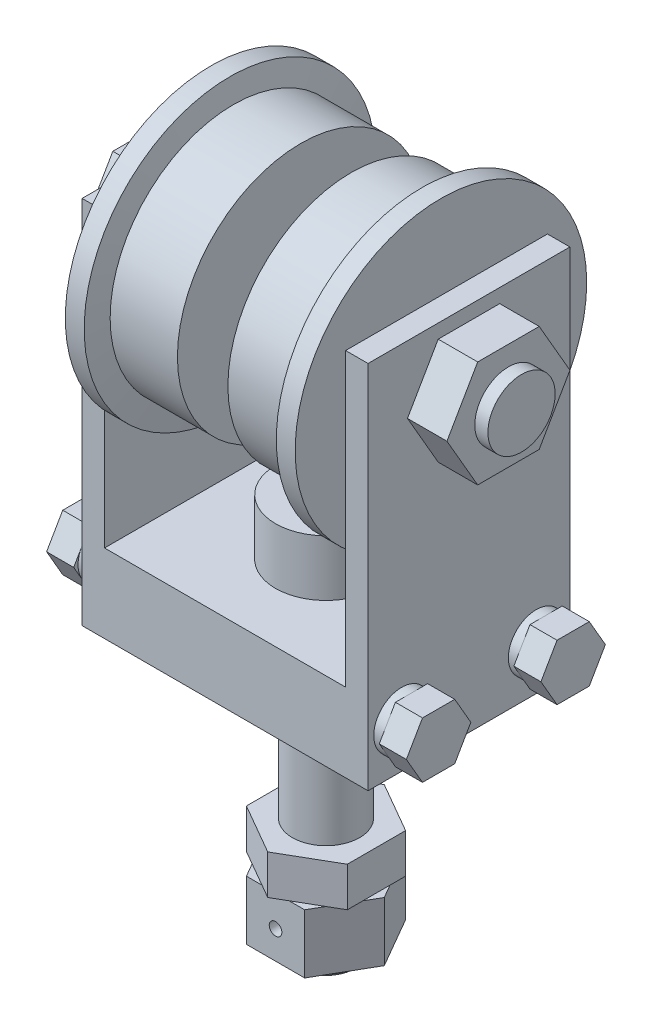
SolidWorks part; units mm, degrees
ref_plane "Front" through (0, 0, 0) normal (0, 0, 1) x (1, 0, 0)
ref_plane "Top" through (0, 0, 0) normal (0, 1, 0) x (1, 0, 0)
ref_plane "Right" through (0, 0, 0) normal (1, 0, 0) x (0, 0, -1)
ref_plane "Z PLANE" through (0, 0, 0) normal (0, 0, 1) x (1, 0, 0)
ref_plane "YOKE BOTTOM" through (0, 0, 0) normal (0, 1, 0) x (-1, 0, 0)
ref_plane "X PLANE" through (0, 0, 0) normal (1, 0, 0) x (0, 0, -1)
sketch "YOKE CROSS SECTION" plane through (0, 0, 0) normal (1, 0, 0) x (0, 0, -1)
  line L0 (0, 0) -> (0, 57.0916) construction
  line L1 (0, 84.8167) -> (0, -84.8167) construction
  line L2 (-57.15, 0) -> (57.15, 0)
  line L3 (69.1602, 0) -> (-69.1602, 0) construction
  line L4 (57.15, 0) -> (57.15, 44.45)
  line L5 (-57.15, 0) -> (-57.15, 44.45)
  line L6 (57.15, 44.45) -> (-57.15, 44.45)
  point P12 (0, 44.45)
  dimension "D1" = 44.45
  dimension "D2" = 114.3
ref_plane "1/2 YOKE LENGTH (A)" through (68.2625, 0, 0) normal (1, 0, 0) x (0, 0, -1)
extrude "YOKE" add sketch "YOKE CROSS SECTION" along normal up to surface (68.2625 mm away) up to plane "1/2 YOKE LENGTH (A)"
sketch "SIDEPLATE PROFILE" plane through (68.2625, 0, 0) normal (1, 0, 0) x (0, 0, -1)
  line L0 (0, 0) -> (0, 74.7424) construction
  line L1 (0, 84.8167) -> (0, -84.8167) construction
  line L2 (-57.15, 0) -> (57.15, 0)
  line L3 (57.15, 0) -> (57.15, 209.55)
  line L4 (-57.15, 0) -> (-57.15, 209.55)
  line L5 (57.15, 209.55) -> (-57.15, 209.55)
  point P11 (0, 209.55)
  dimension "D1" = 209.55
ref_plane "WHEEL HEIGHT" through (0, 171.45, 0) normal (0, 1, 0) x (-1, 0, 0)
ref_plane "SCREW LOCATION X" through (0, 0, 38.1) normal (0, 0, 1) x (1, 0, 0)
ref_plane "SCREW LOCATION Y" through (0, 25.4, 0) normal (0, 1, 0) x (-1, 0, 0)
extrude "SIDEPLATE" add sketch "SIDEPLATE PROFILE" along normal blind 12.7
sketch "WHEEL PIN NUT PROFILE" plane through (80.9625, 0, 0) normal (1, 0, 0) x (0, 0, -1)
  line L0 (0, 84.8167) -> (0, -84.8167) construction
  line L1 (34.8287, 171.45) -> (17.4143, 201.6125)
  line L2 (17.4143, 201.6125) -> (-17.4143, 201.6125)
  line L3 (-17.4143, 201.6125) -> (-34.8287, 171.45)
  line L4 (-34.8287, 171.45) -> (-17.4143, 141.2875)
  line L5 (-17.4143, 141.2875) -> (17.4143, 141.2875)
  line L6 (17.4143, 141.2875) -> (34.8287, 171.45)
  line L7 (69.1602, 171.45) -> (-69.1602, 171.45) construction
  circle A0 centre (0, 171.45) radius 30.1625 construction
  dimension "D1" = 60.325
extrude "WHEEL PIN NUT" add sketch "WHEEL PIN NUT PROFILE" along normal blind 22.352
sketch "WHEEL PIN PROJECTION PROFILE" plane through (103.3145, 0, 0) normal (1, 0, 0) x (0, 0, -1)
  line L0 (0, 84.8167) -> (0, -84.8167) construction
  line L1 (69.1602, 171.45) -> (-69.1602, 171.45) construction
  circle A0 centre (0, 171.45) radius 19.05
  dimension "D1" = 38.1
extrude "WHEEL PIN PROJECTION" add sketch "WHEEL PIN PROJECTION PROFILE" along normal blind 7.4168
sketch "LOCKNUTS PROFILE" plane through (80.9625, 0, 0) normal (1, 0, 0) x (0, 0, -1)
  line L0 (-38.1, 84.8167) -> (-38.1, -84.8167) construction
  line L1 (50, 25.4) -> (-50, 25.4) construction
  circle A0 centre (-38.1, 25.4) radius 15.8115
  dimension "D1" = 31.623
extrude "LOCKNUTS" add sketch "LOCKNUTS PROFILE" along normal blind 5.5626
sketch "SCREWS PROFILE" plane through (86.5251, 0, 0) normal (1, 0, 0) x (0, 0, -1)
  line L0 (50, 25.4) -> (-50, 25.4) construction
  line L1 (-19.8425, 25.4) -> (-28.9712, 41.2115)
  line L2 (-28.9712, 41.2115) -> (-47.2288, 41.2115)
  line L3 (-47.2288, 41.2115) -> (-56.3575, 25.4)
  line L4 (-56.3575, 25.4) -> (-47.2288, 9.5885)
  line L5 (-47.2288, 9.5885) -> (-28.9712, 9.5885)
  line L6 (-28.9712, 9.5885) -> (-19.8425, 25.4)
  line L7 (-38.1, 84.8167) -> (-38.1, -84.8167) construction
  circle A0 centre (-38.1, 25.4) radius 15.8115 construction
  dimension "D1" = 31.623
extrude "SCREWS" add sketch "SCREWS PROFILE" along normal blind 15.3416
sketch "PROFILE" plane through (0, 44.45, 0) normal (0, 1, 0) x (-1, 0, 0)
  line L0 (84.8167, 0) -> (-84.8167, 0) construction
  line L1 (0, 83.2389) -> (0, -83.2389) construction
  circle A0 centre (0, 0) radius 28.575
  dimension "D1" = 57.15
extrude "KING BOLT HEAD" add sketch "PROFILE" along normal blind 31.75
mirror "Mirror1" about plane through (0, 0, 0) normal (0, 0, 1) of "SCREWS", "LOCKNUTS"
mirror "Mirror5" about plane through (0, 0, 0) normal (1, 0, 0) of bodies 112
ref_plane "TOP OF NUT" through (0, -82.55, 0) normal (0, 1, 0) x (-1, 0, 0)
sketch "DIA." plane through (0, 0, 0) normal (0, -1, 0) x (1, 0, 0)
  line L0 (84.8167, 0) -> (-84.8167, 0) construction
  line L1 (0, -83.2389) -> (0, 83.2389) construction
  circle A0 centre (0, 0) radius 19.05
  dimension "D1" = 38.1
extrude "KING BOLT" add sketch "DIA." along normal up to surface (82.55 mm away) up to plane "TOP OF NUT"
sketch "KING BOLT JAN NUT PROFILE" plane through (0, -82.55, 0) normal (0, -1, 0) x (1, 0, 0)
  line L0 (84.8167, 0) -> (-84.8167, 0) construction
  line L1 (0, -32.9956) -> (28.575, -16.4978)
  line L2 (28.575, -16.4978) -> (28.575, 16.4978)
  line L3 (28.575, 16.4978) -> (0, 32.9956)
  line L4 (0, 32.9956) -> (-28.575, 16.4978)
  line L5 (-28.575, 16.4978) -> (-28.575, -16.4978)
  line L6 (-28.575, -16.4978) -> (0, -32.9956)
  line L7 (0, -83.2389) -> (0, 83.2389) construction
  circle A0 centre (0, 0) radius 28.575 construction
  dimension "D1" = 57.15
extrude "KING BOLT JAM NUT" add sketch "KING BOLT JAN NUT PROFILE" along normal blind 22.352
sketch "KING BOLT NUT PROFILE" plane through (0, -104.902, 0) normal (0, -1, 0) x (1, 0, 0)
  line L1 (32.9956, 0) -> (16.4978, 28.575)
  line L2 (16.4978, 28.575) -> (-16.4978, 28.575)
  line L3 (-16.4978, 28.575) -> (-32.9956, 0)
  line L4 (-32.9956, 0) -> (-16.4978, -28.575)
  line L5 (-16.4978, -28.575) -> (16.4978, -28.575)
  line L6 (16.4978, -28.575) -> (32.9956, 0)
  line L10 (0, -83.2389) -> (0, 83.2389) construction
  line L11 (84.8167, 0) -> (-84.8167, 0) construction
  circle A0 centre (0, 0) radius 28.575 construction
  dimension "D1" = 57.15
extrude "KING BOLT NUT" add sketch "KING BOLT NUT PROFILE" along normal blind 33.4518
sketch "Sketch5" plane through (0, -138.3538, 0) normal (0, -1, 0) x (1, 0, 0)
  circle A0 centre (0, 0) radius 19.05 construction
  circle A1 centre (0, 0) radius 19.05
extrude "EXTENDED KING BOLT" add sketch "Sketch5" along normal blind 9.525
chamfer "Chamfer1" distance 2.3812 angle 45 1 edges at (0, -147.8788, -19.05)
ref_plane "MOUNTING REF PLANE" through (0, -34.925, 0) normal (0, 1, 0) x (-1, 0, 0)
sketch "Sketch6" plane through (0, 0, 0) normal (0, 0, 1) x (1, 0, 0)
  line L0 (65.0875, 198.4375) -> (65.0875, 254)
  line L1 (52.3875, 241.3) -> (54.399, 254)
  line L2 (68.2625, 171.45) -> (14.2875, 171.45)
  line L3 (14.2875, 171.45) -> (14.2875, 241.3)
  line L4 (68.2625, 171.45) -> (68.2625, 198.4375)
  line L5 (68.2625, 198.4375) -> (68.2625, 171.45)
  line L6 (68.2625, 198.4375) -> (65.0875, 198.4375)
  line L7 (54.399, 254) -> (65.0875, 254)
  line L8 (69.1602, 171.45) -> (-69.1602, 171.45) construction
  line L9 (68.2625, -75.0522) -> (68.2625, 75.0522) construction
  line L10 (52.3875, 241.3) -> (14.2875, 241.3)
  dimension "D1" = 3.175
  dimension "D2" = 13.8635
  dimension "D3" = 15.875
  dimension "D4" = 53.975
  dimension "D5" = 26.9875
  dimension "D6" = 82.55
  dimension "D7" = 69.85
revolve "WHEEL" add sketch "Sketch6" angle 360 about L2
mirror "Mirror6" about plane through (0, 0, 0) normal (1, 0, 0) of "WHEEL"
sketch "Sketch7" plane through (0, 0, 28.575) normal (0, 0, 1) x (1, 0, 0)
  line L0 (0, -83.2389) -> (0, 83.2389) construction
  line L1 (-16.4978, -138.3538) -> (-32.9956, -138.3538) construction
  circle A0 centre (0, -122.4788) radius 3.5719
  dimension "D1" = 7.1437
  dimension "D2" = 15.875
extrude "COTTER PIN HOLE" cut sketch "Sketch7" against normal up to next
sketch "Sketch8" plane through (0, 0, 0) normal (0, -1, 0) x (1, 0, 0)
  circle A0 centre (0, 0) radius 25.4
  circle A1 centre (0, 0) radius 30.1625
  dimension "D1" = 50.8
  dimension "D2" = 60.325
extrude "SPACER" [suppressed] add sketch "Sketch8" along normal blind 12.7
ref_plane "TREAD OF TRACK" through (0, 101.6, 0) normal (0, 1, 0) x (-1, 0, 0)
